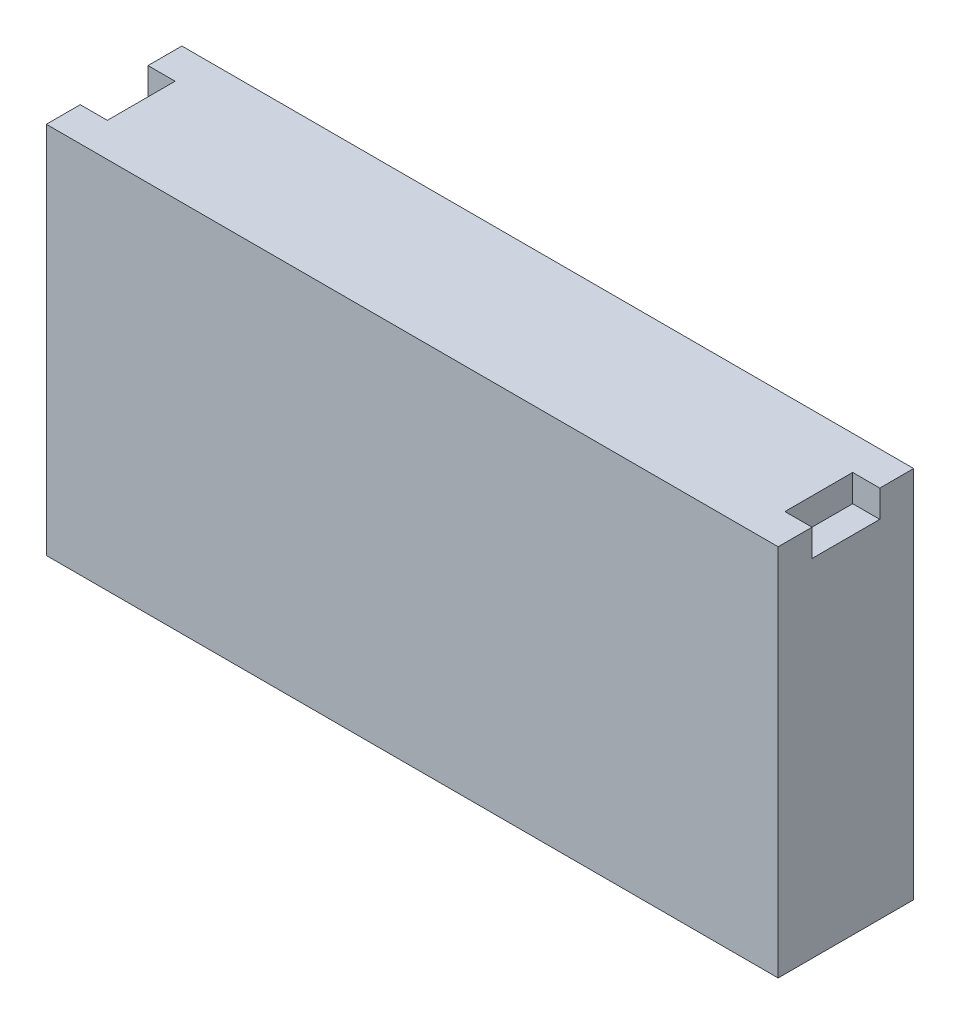
SolidWorks part; units mm, degrees
ref_plane "Front Plane" through (0, 0, 0) normal (0, 0, 1) x (1, 0, 0)
ref_plane "Top Plane" through (0, 0, 0) normal (0, 1, 0) x (1, 0, 0)
ref_plane "Right Plane" through (0, 0, 0) normal (1, 0, 0) x (0, 0, -1)
sketch "Sketch1" plane through (0, 0, 0) normal (0, 1, 0) x (1, 0, 0)
  line L1 (-342.9, 63.5) -> (342.9, 63.5)
  line L2 (-342.9, 63.5) -> (-342.9, -63.5)
  line L3 (-342.9, -63.5) -> (342.9, -63.5)
  line L4 (342.9, 63.5) -> (342.9, -63.5)
  line L5 (-342.9, 63.5) -> (342.9, -63.5) construction
  line L6 (-342.9, -63.5) -> (342.9, 63.5) construction
  point P0 (0, 0)
  dimension "D1" = 685.8
  dimension "D2" = 127
extrude "Boss-Extrude1" add sketch "Sketch1" along normal blind 350
sketch "Sketch2" plane through (0, 350, 0) normal (0, 1, 0) x (1, 0, 0)
  line L0 (-342.9, 63.5) -> (-342.9, -63.5) construction
  line L5 (-342.9, 31.75) -> (-317.5, 31.75)
  line L6 (-342.9, 31.75) -> (-342.9, -31.75)
  line L7 (-342.9, -31.75) -> (-317.5, -31.75)
  line L8 (-317.5, 31.75) -> (-317.5, -31.75)
  line L9 (0, -55) -> (0, 55) construction
  line L10 (342.9, -31.75) -> (317.5, -31.75)
  line L11 (317.5, 31.75) -> (317.5, -31.75)
  line L12 (342.9, 31.75) -> (317.5, 31.75)
  line L13 (342.9, 31.75) -> (342.9, -31.75)
  point P6 (-342.9, 0)
  point P7 (-342.9, 0)
  dimension "D1" = 63.5
  dimension "D2" = 25.4
extrude "Cut-Extrude2" cut sketch "Sketch2" against normal blind 25.4
